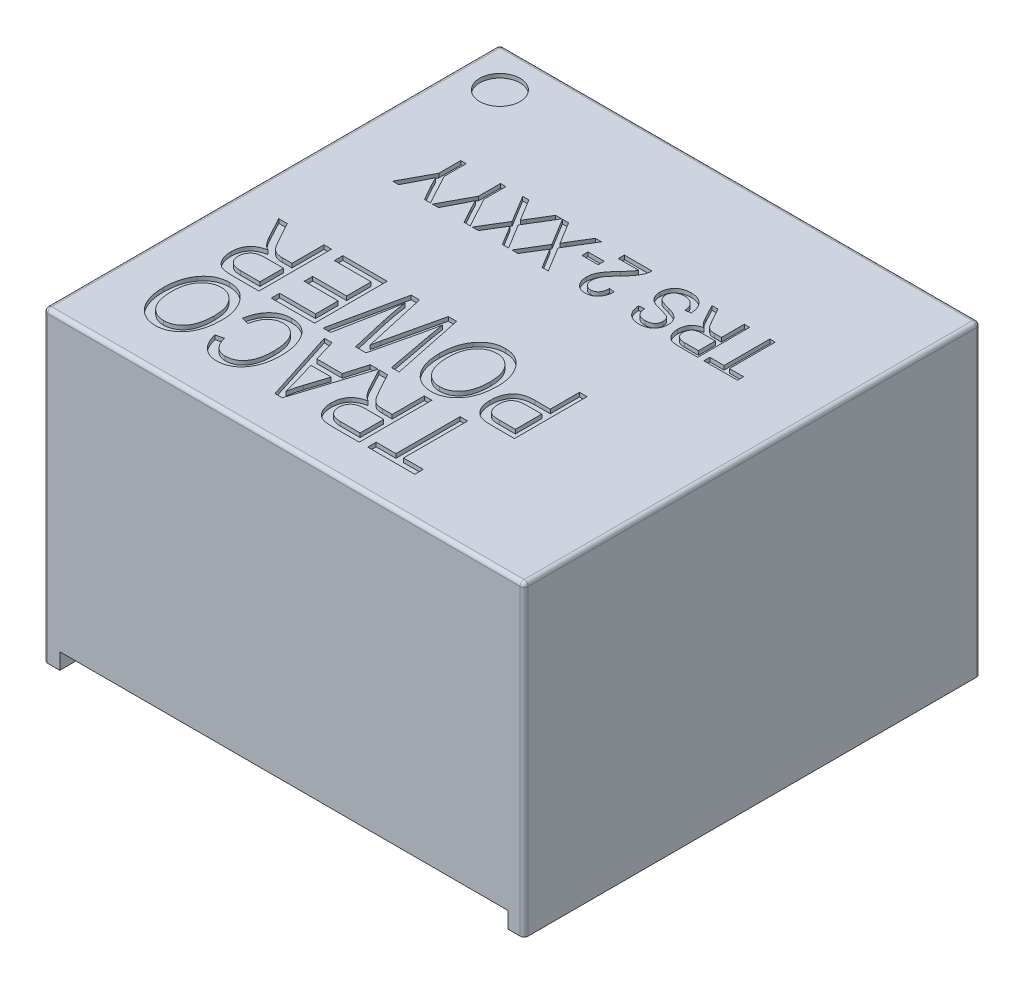
SolidWorks part; units mm, degrees
ref_plane "Front Plane" through (0, 0, 0) normal (0, 0, 1) x (1, 0, 0)
ref_plane "Top Plane" through (0, 0, 0) normal (0, 1, 0) x (1, 0, 0)
ref_plane "Right Plane" through (0, 0, 0) normal (1, 0, 0) x (0, 0, -1)
sketch "Sketch1" plane through (0, 0, 0) normal (0, 1, 0) x (1, 0, 0)
  line L1 (-5.95, -5.65) -> (5.95, -5.65)
  line L2 (-5.95, -5.65) -> (-5.95, 5.65)
  line L3 (-5.95, 5.65) -> (5.95, 5.65)
  line L4 (5.95, -5.65) -> (5.95, 5.65)
  line L5 (-5.95, -5.65) -> (5.95, 5.65) construction
  line L6 (-5.95, 5.65) -> (5.95, -5.65) construction
  point P0 (0, 0)
  dimension "D1" = 11.9
  dimension "D2" = 11.3
extrude "Boss-Extrude1" add sketch "Sketch1" along normal blind 7.6
sketch "Sketch3" plane through (0, 0, 5.65) normal (0, 0, 1) x (1, 0, 0)
  line L0 (-5.95, 0) -> (5.95, 0) construction
  line L1 (-5.55, 0) -> (5.55, 0)
  line L2 (-5.55, 0) -> (-5.55, 0.4)
  line L3 (-5.55, 0.4) -> (5.55, 0.4)
  line L4 (5.55, 0) -> (5.55, 0.4)
  line L5 (-5.95, 7.6) -> (-5.95, 0) construction
  line L6 (5.95, 7.6) -> (5.95, 0) construction
  dimension "D1" = 0.4
  dimension "D2" = 0.4
  dimension "D3" = 0.4
extrude "Cut-Extrude2" cut sketch "Sketch3" against normal through all
sketch "Sketch4" plane through (0, 0.4, 0) normal (0, -1, 0) x (1, 0, 0)
  line L0 (5.55, -5.65) -> (5.55, 5.65) construction
  line L1 (-5.55, 5.25) -> (5.55, 5.25)
  line L2 (-5.55, 5.25) -> (-5.55, -5.25)
  line L3 (-5.55, -5.25) -> (5.55, -5.25)
  line L4 (5.55, 5.25) -> (5.55, -5.25)
  line L5 (-5.55, 5.25) -> (5.55, -5.25) construction
  line L6 (-5.55, -5.25) -> (5.55, 5.25) construction
  line L7 (5.55, 5.65) -> (-5.55, 5.65) construction
  point P0 (0, 0)
  dimension "D1" = 0.4
extrude "Cut-Extrude3" cut sketch "Sketch4" against normal blind 0.1
fillet "Fillet1" radius 0.1 9 edges at (-5.95, 0, 0) (5.95, 3.8, -5.65) (5.95, 3.8, 5.65) (0, 7.6, 5.65) (5.95, 7.6, 0) (0, 7.6, -5.65) (-5.95, 3.8, 5.65) (-5.95, 7.6, 0) (-5.95, 3.8, -5.65)
sketch "Sketch5" plane through (0, 7.6, 0) normal (0, 1, 0) x (1, 0, 0)
  line L0 (-5.85, 5.65) -> (5.85, 5.65) construction
  line L1 (-5.95, -5.55) -> (-5.95, 5.55) construction
  circle A0 centre (-4.95, 4.65) radius 0.5
  dimension "D3" = 1
  dimension "D1" = 1
  dimension "D2" = 1
extrude "Cut-Extrude4" cut sketch "Sketch5" against normal blind 0.1
sketch "Sketch6" plane through (0, 7.6, 0) normal (0, 1, 0) x (1, 0, 0)
  line L0 (4.85, 2.65) -> (-4.95, 2.65) construction
  line L1 (5.85, 5.55) -> (-5.85, 5.55) construction
  line L2 (-5.85, 5.65) -> (5.85, 5.65) construction
  line L3 (5.85, -5.55) -> (5.85, 5.55) construction
  line L5 (-5.95, -5.55) -> (-5.95, 5.55) construction
  line L6 (4.85, -0.85) -> (-4.95, -0.85) construction
  line L7 (4.85, -2.85) -> (-4.95, -2.85) construction
  text T0 "TRS 2-XXYY" font "Arial Narrow" height in points 5
  text T1 "POWER" font "Arial Narrow" height in points 7
  text T2 "TRACO" font "Arial Narrow" height in points 7
  point P13 (0, 0)
  point P14 (0, 0)
  dimension "D1" = 3
  dimension "D2" = 1
  dimension "D3" = 1
  dimension "D4" = 3.5
  dimension "D5" = 2
extrude "Cut-Extrude5" cut sketch "Sketch6" against normal blind 0.1
